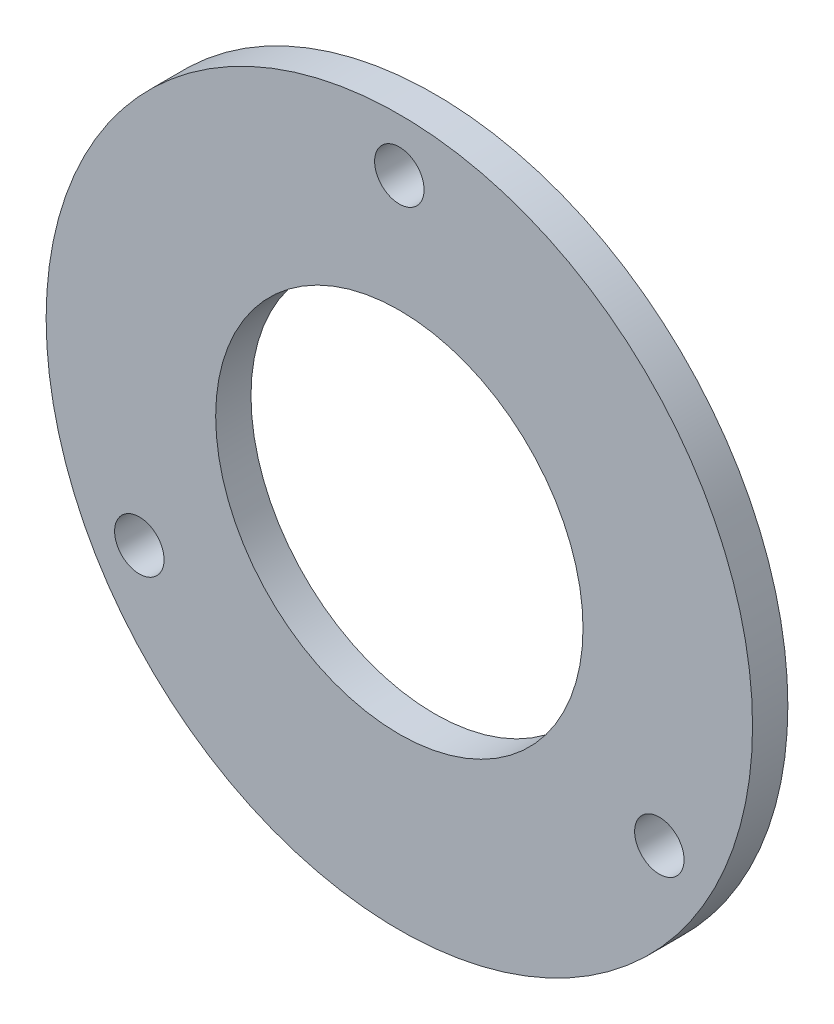
SolidWorks part; units mm, degrees
ref_plane "Płaszczyzna przednia" through (0, 0, 0) normal (0, 0, 1) x (1, 0, 0)
ref_plane "Płaszczyzna górna" through (0, 0, 0) normal (0, 1, 0) x (1, 0, 0)
ref_plane "Płaszczyzna prawa" through (0, 0, 0) normal (1, 0, 0) x (0, 0, -1)
sketch "Szkic1" plane through (0, 0, 0) normal (0, 0, 1) x (1, 0, 0)
  circle A0 centre (0, 0) radius 50
  circle A1 centre (0, 0) radius 26
  dimension "D1" = 100
  dimension "D2" = 52
extrude "Dodanie-wyciągnięcie1" add sketch "Szkic1" along normal blind 5
sketch "Szkic3" plane through (0, 0, 5) normal (0, 0, 1) x (1, 0, 0)
  circle A0 centre (0, 42.5) radius 3.5
  circle A3 centre (36.8061, -21.25) radius 3.5
  circle A4 centre (-36.8061, -21.25) radius 3.5
  point P14 (0, 0)
  dimension "D1" = 7
  dimension "D2" = 42.5
  dimension "D6" = 3
extrude "Wytnij-wyciągnięcie4" cut sketch "Szkic3" against normal through all both and the other way through all
